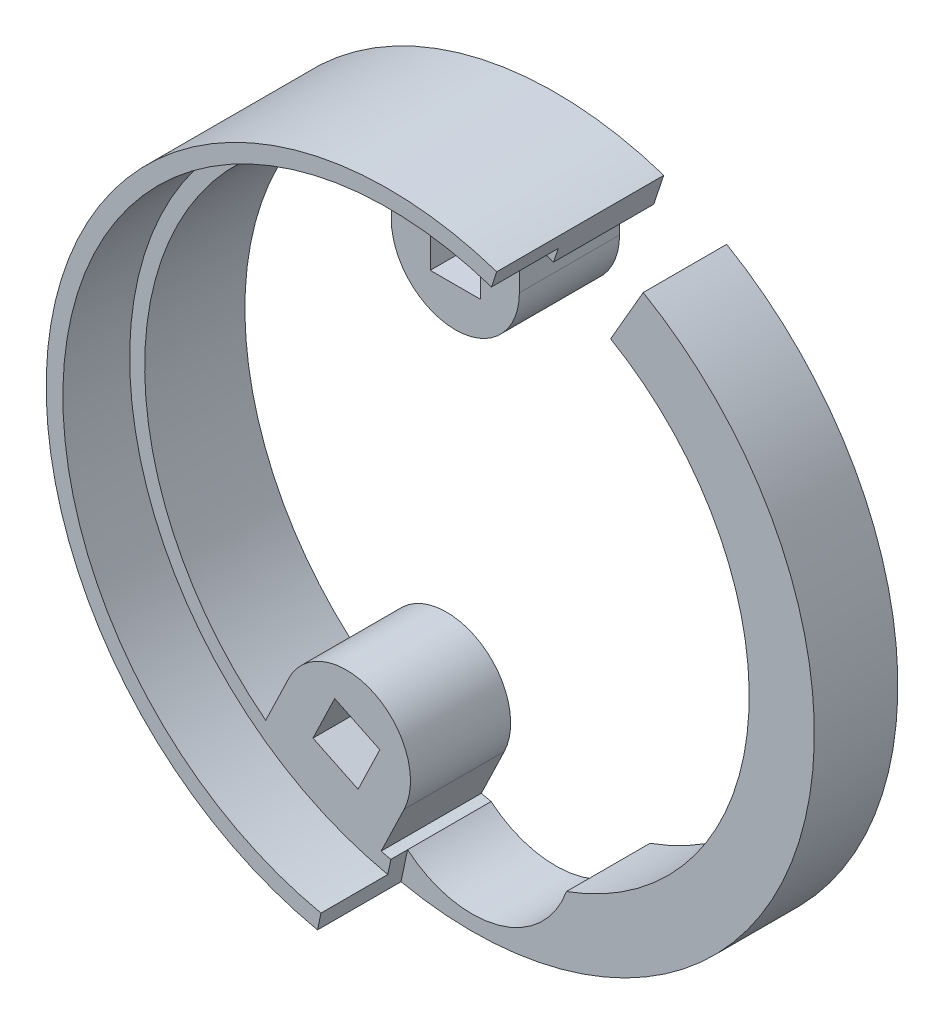
SolidWorks part; units mm, degrees
ref_plane "Plano frontal" through (0, 0, 0) normal (0, 0, 1) x (1, 0, 0)
ref_plane "Plano superior" through (0, 0, 0) normal (0, 1, 0) x (1, 0, 0)
ref_plane "Plano direito" through (0, 0, 0) normal (1, 0, 0) x (0, 0, -1)
sketch "Esboço2" plane through (0, 0, 0) normal (0, 0, 1) x (1, 0, 0)
  circle A0 centre (0, 0) radius 18.6
  circle A1 centre (0, 0) radius 17.6
  circle A2 centre (0, 0) radius 16.6
  arc A3 (8.0554, 16.2087) -> (-8.0554, 16.2087) centre (0, 0) ccw
sketch "Esboço4" plane through (0, 0, 0) normal (0, 0, 1) x (1, 0, 0)
  line L1 (8.3, 14.376) -> (10.25, 17.7535)
  line L2 (0, 0) -> (0, -20.5) construction
  line L3 (0, -20.5) -> (0, -19.6) construction
  line L4 (5.882, 17.6454) -> (6.4829, 19.4479)
  arc A0 (6.4829, 19.4479) -> (10.25, 17.7535) centre (0, 0) ccw
  arc A1 (-3.8575, -18.1956) -> (5.6542, -15.6074) centre (0, -13.6) ccw
  arc A2 (5.6106, -15.6231) -> (8.3, 14.376) centre (0, 0) ccw
  circle A3 centre (0, 0) radius 18.6 construction
  arc A4 (5.882, 17.6454) -> (-3.8575, -18.1956) centre (0, 0) ccw
  dimension "D1" = 12
  dimension "D2" = 0.9
extrude "Ressalto-extrusão2" add sketch "Esboço4" along normal blind 6 contours A4 L4 A0 L1 A2 A1
sketch "Esboço6" plane through (0, 0, 0) normal (0, 0, -1) x (-1, 0, 0)
  circle A0 centre (0, 0) radius 20.5
sketch "Esboço7" plane through (0, 0, 6) normal (0, 0, 1) x (1, 0, 0)
  line L1 (-3.8575, -18.1956) -> (-4.2516, -20.0543)
  line L2 (5.882, 17.6454) -> (6.4829, 19.4479)
  line L3 (10.25, 17.7535) -> (8.3, 14.376)
  line L5 (10.25, 17.7535) -> (8.3, 14.376)
  arc A4 (5.882, 17.6454) -> (-3.8575, -18.1956) centre (0, 0) ccw
  arc A5 (6.4829, 19.4479) -> (10.25, 17.7535) centre (0, 0) ccw
  arc A6 (5.6542, -15.6074) -> (8.3, 14.376) centre (0, 0) ccw
  arc A7 (-3.8575, -18.1956) -> (5.6542, -15.6074) centre (0, -13.6) ccw
  arc A9 (-4.2516, -20.0543) -> (10.25, 17.7535) centre (0, 0) ccw
  arc A10 (5.6542, -15.6074) -> (8.3, 14.376) centre (0, 0) ccw
  arc A11 (-3.8575, -18.1956) -> (5.6542, -15.6074) centre (0, -13.6) ccw
  dimension "D1" = 0
extrude "Corte-extrusão1" cut sketch "Esboço7" against normal blind 1
sketch "Esboço8" plane through (0, 0, 0) normal (0, 0, -1) x (-1, 0, 0)
  line L0 (11.5128, 7.2626) -> (9.6423, 9.6081) [skipped]
  line L1 (11.5128, 7.2626) -> (13.8583, 9.133) [skipped]
  line L2 (0, 0) -> (0, 19.7756) construction
  line L3 (13.8583, 9.133) -> (11.9878, 11.4785) [skipped]
  line L4 (9.6423, 9.6081) -> (11.9878, 11.4785) [skipped]
  line L5 (14.1416, 6.3719) -> (17.6322, 9.1555) [skipped]
  line L6 (17.6322, 9.1555) -> (12.8495, 15.1528) [skipped]
  line L7 (12.8495, 15.1528) -> (9.3589, 12.3692) [skipped]
  line L8 (0, 0) -> (15.4612, 12.3299) construction
  line L9 (11.5128, 7.2626) -> (11.9878, 11.4785) construction
  line L10 (13.8583, 9.133) -> (9.6423, 9.6081) construction
  line L11 (12.8562, -4.4729) -> (13.5238, -1.5481) [skipped]
  line L12 (12.8562, -4.4729) -> (15.781, -5.1405) [skipped]
  line L13 (15.781, -5.1405) -> (16.4485, -2.2157) [skipped]
  line L14 (13.5238, -1.5481) -> (16.4485, -2.2157) [skipped]
  line L15 (13.7989, -7.0836) -> (18.1516, -8.077) [skipped]
  line L16 (18.1516, -8.077) -> (19.8585, -0.5985) [skipped]
  line L17 (19.8585, -0.5985) -> (15.5058, 0.3949) [skipped]
  line L18 (0, 0) -> (19.2797, -4.4005) construction
  line L19 (12.8562, -4.4729) -> (16.4485, -2.2157) construction
  line L20 (15.781, -5.1405) -> (13.5238, -1.5481) construction
  line L21 (4.5186, -12.8402) -> (7.2215, -11.5386)
  line L22 (1.5, 13.5292) -> (-1.5, 13.5292)
  line L23 (1.5, 13.5292) -> (1.5, 16.5292)
  line L24 (1.5, 16.5292) -> (-1.5, 16.5292)
  line L25 (-1.5, 13.5292) -> (-1.5, 16.5292)
  line L26 (1.5, 13.5292) -> (-1.5, 16.5292) construction
  line L27 (1.5, 16.5292) -> (-1.5, 13.5292) construction
  line L28 (4.5186, -12.8402) -> (5.8203, -15.5431)
  line L29 (5.8203, -15.5431) -> (8.5232, -14.2415)
  line L30 (7.2215, -11.5386) -> (8.5232, -14.2415)
  line L31 (3.0653, -15.205) -> (5.0025, -19.2274)
  line L32 (5.0025, -19.2274) -> (11.9136, -15.8992)
  line L33 (11.9136, -15.8992) -> (9.9765, -11.8767)
  line L34 (0, 0) -> (8.5803, -17.8172) construction
  line L35 (4.5186, -12.8402) -> (8.5232, -14.2415) construction
  line L36 (5.8203, -15.5431) -> (7.2215, -11.5386) construction
  line L37 (-7.2215, -11.5386) -> (-4.5186, -12.8402) [skipped]
  line L38 (-7.2215, -11.5386) -> (-8.5232, -14.2415) [skipped]
  line L39 (-8.5232, -14.2415) -> (-5.8203, -15.5431) [skipped]
  line L40 (-4.5186, -12.8402) -> (-5.8203, -15.5431) [skipped]
  line L41 (-9.9765, -11.8767) -> (-11.9136, -15.8992) [skipped]
  line L42 (-11.9136, -15.8992) -> (-5.0025, -19.2274) [skipped]
  line L43 (-5.0025, -19.2274) -> (-3.0653, -15.205) [skipped]
  line L44 (0, 0) -> (-8.5803, -17.8172) construction
  line L45 (-7.2215, -11.5386) -> (-5.8203, -15.5431) construction
  line L46 (-8.5232, -14.2415) -> (-4.5186, -12.8402) construction
  line L47 (-13.5238, -1.5481) -> (-12.8562, -4.4729) [skipped]
  line L48 (-13.5238, -1.5481) -> (-16.4485, -2.2157) [skipped]
  line L49 (3.8354, 15.0292) -> (3.8354, 19.4938)
  line L50 (3.8354, 19.4938) -> (-3.8354, 19.4938)
  line L51 (-3.8354, 19.4938) -> (-3.8354, 15.0292)
  line L52 (-16.4485, -2.2157) -> (-15.781, -5.1405) [skipped]
  line L53 (-12.8562, -4.4729) -> (-15.781, -5.1405) [skipped]
  line L54 (-15.5058, 0.3949) -> (-19.8585, -0.5985) [skipped]
  line L55 (-19.8585, -0.5985) -> (-18.1516, -8.077) [skipped]
  line L56 (-18.1516, -8.077) -> (-13.7989, -7.0836) [skipped]
  line L57 (0, 0) -> (-19.2797, -4.4005) construction
  line L58 (-13.5238, -1.5481) -> (-15.781, -5.1405) construction
  line L59 (-16.4485, -2.2157) -> (-12.8562, -4.4729) construction
  line L60 (-9.6423, 9.6081) -> (-11.5128, 7.2626) [skipped]
  line L61 (-9.6423, 9.6081) -> (-11.9878, 11.4785) [skipped]
  line L62 (-11.9878, 11.4785) -> (-13.8583, 9.133) [skipped]
  line L63 (-11.5128, 7.2626) -> (-13.8583, 9.133) [skipped]
  line L64 (-9.3589, 12.3692) -> (-12.8495, 15.1528) [skipped]
  line L65 (-12.8495, 15.1528) -> (-17.6322, 9.1555) [skipped]
  line L66 (-17.6322, 9.1555) -> (-14.1416, 6.3719) [skipped]
  line L67 (0, 0) -> (-15.4612, 12.3299) construction
  line L68 (-9.6423, 9.6081) -> (-13.8583, 9.133) construction
  line L69 (-11.9878, 11.4785) -> (-11.5128, 7.2626) construction
  arc A0 (9.3589, 12.3692) -> (14.1416, 6.3719) centre (11.7503, 9.3705) ccw [skipped]
  arc A1 (15.5058, 0.3949) -> (13.7989, -7.0836) centre (14.6524, -3.3443) ccw [skipped]
  arc A2 (9.9765, -11.8767) -> (3.0653, -15.205) centre (6.5209, -13.5408) ccw
  arc A3 (-3.0653, -15.205) -> (-9.9765, -11.8767) centre (-6.5209, -13.5408) ccw [skipped]
  arc A4 (-13.7989, -7.0836) -> (-15.5058, 0.3949) centre (-14.6524, -3.3443) ccw [skipped]
  arc A5 (-3.8354, 15.0292) -> (3.8354, 15.0292) centre (0, 15.0292) ccw
  arc A6 (-14.1416, 6.3719) -> (-9.3589, 12.3692) centre (-11.7503, 9.3705) ccw [skipped]
  point P14 (11.7503, 9.3705)
  point P20 (0, 0)
  point P24 (0, 15.0292)
  point P32 (14.6524, -3.3443)
  point P37 (0, 0)
  point P44 (6.5209, -13.5408)
  point P49 (0, 0)
  point P56 (-6.5209, -13.5408)
  point P61 (0, 0)
  point P68 (-14.6524, -3.3443)
  point P69 (0, 0)
  point P75 (0, 0)
  point P82 (-11.7503, 9.3705)
  point P87 (0, 0)
  point P89 (0, 0)
  dimension "D1" = 7
extrude "Ressalto-extrusão4" add sketch "Esboço8" against normal up to surface (6 mm away)
sketch "Esboço9" plane through (0, 0, 6) normal (0, 0, 1) x (1, 0, 0)
  line L0 (-4.0442, -19.076) -> (-4.2516, -20.0543)
  line L1 (6.1667, 18.4993) -> (6.4829, 19.4479)
  arc A1 (6.4829, 19.4479) -> (-4.2516, -20.0543) centre (0, 0) ccw
  arc A2 (6.1667, 18.4993) -> (-4.0442, -19.076) centre (0, 0) ccw
  dimension "D1" = 1
extrude "Ressalto-extrusão5" add sketch "Esboço9" along normal blind 4
